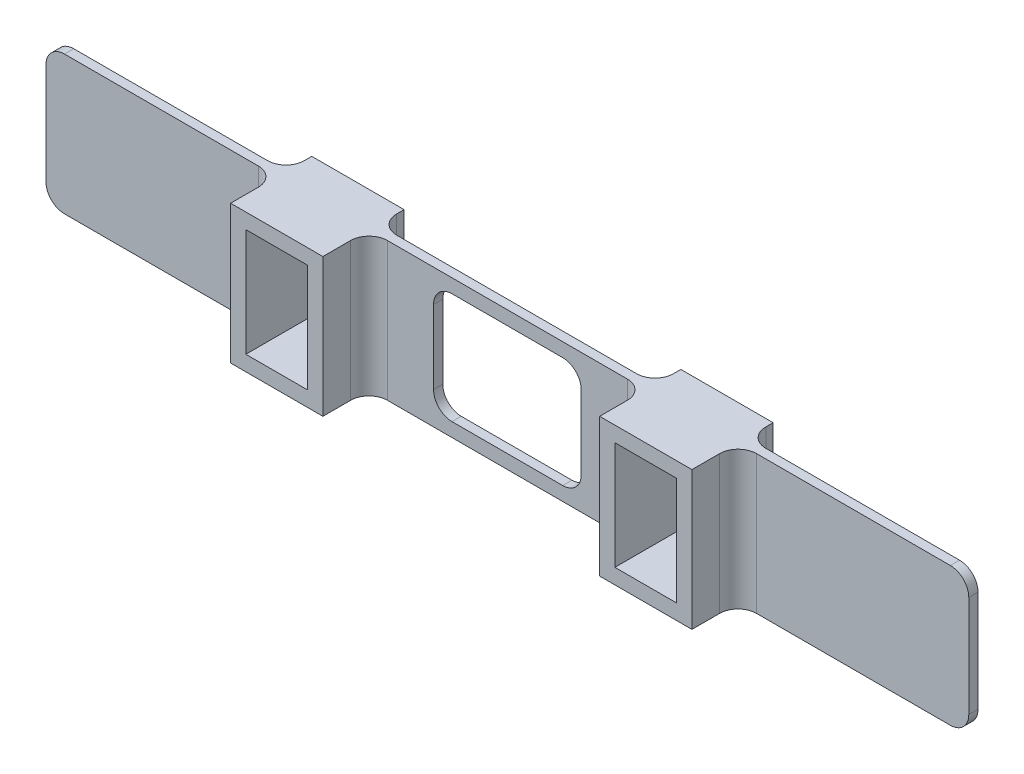
SolidWorks part; units mm, degrees
ref_plane "Front Plane" through (0, 0, 0) normal (0, 0, 1) x (1, 0, 0)
ref_plane "Top Plane" through (0, 0, 0) normal (0, 1, 0) x (1, 0, 0)
ref_plane "Right Plane" through (0, 0, 0) normal (1, 0, 0) x (0, 0, -1)
sketch "Sketch1" plane through (0, 0, 0) normal (0, 0, 1) x (1, 0, 0)
  line L1 (-250, -37.5) -> (250, -37.5)
  line L2 (-250, -37.5) -> (-250, 37.5)
  line L3 (-250, 37.5) -> (250, 37.5)
  line L4 (250, -37.5) -> (250, 37.5)
  line L5 (-250, -37.5) -> (250, 37.5) construction
  line L6 (-250, 37.5) -> (250, -37.5) construction
  point P0 (0, 0)
extrude "Boss-Extrude1" add sketch "Sketch1" along normal blind 5
sketch "Sketch2" plane through (0, 0, 5) normal (0, 0, 1) x (1, 0, 0)
  line L3 (-116.7208, -29.25) -> (-83.2208, -29.25)
  line L4 (-116.7208, -29.25) -> (-116.7208, 29.25)
  line L5 (-116.7208, 29.25) -> (-83.2208, 29.25)
  line L6 (-83.2208, -29.25) -> (-83.2208, 29.25)
  line L9 (83.25, -29.2517) -> (116.75, -29.2517)
  line L10 (83.25, -29.2517) -> (83.25, 29.2517)
  line L11 (83.25, 29.2517) -> (116.75, 29.2517)
  line L12 (116.75, -29.2517) -> (116.75, 29.2517)
extrude "Cut-Extrude1" cut sketch "Sketch2" against normal blind 5
sketch "Sketch3" plane through (0, 0, 5) normal (0, 0, 1) x (1, 0, 0)
  line L0 (250, 37.5) -> (-250, 37.5) construction
  line L1 (-116.7208, -29.25) -> (-83.2208, -29.25)
  line L2 (-116.7208, -29.25) -> (-116.7208, 29.25)
  line L3 (-116.7208, 29.25) -> (-83.2208, 29.25)
  line L4 (-83.2208, -29.25) -> (-83.2208, 29.25)
  line L5 (-116.7208, -29.25) -> (-83.2208, 29.25) construction
  line L6 (-116.7208, 29.25) -> (-83.2208, -29.25) construction
  line L7 (-124.9708, -37.5) -> (-74.9708, -37.5)
  line L8 (-124.9708, -37.5) -> (-124.9708, 37.5)
  line L9 (-124.9708, 37.5) -> (-74.9708, 37.5)
  line L10 (-74.9708, -37.5) -> (-74.9708, 37.5)
  line L11 (-124.9708, -37.5) -> (-74.9708, 37.5) construction
  line L12 (-124.9708, 37.5) -> (-74.9708, -37.5) construction
  line L14 (83.25, -29.2517) -> (116.75, -29.2517)
  line L15 (83.25, -29.2517) -> (83.25, 29.2517)
  line L16 (83.25, 29.2517) -> (116.75, 29.2517)
  line L17 (116.75, -29.2517) -> (116.75, 29.2517)
  line L18 (83.25, -29.2517) -> (116.75, 29.2517) construction
  line L19 (83.25, 29.2517) -> (116.75, -29.2517) construction
  line L20 (75, -37.5) -> (125, -37.5)
  line L21 (75, -37.5) -> (75, 37.5)
  line L22 (75, 37.5) -> (125, 37.5)
  line L23 (125, -37.5) -> (125, 37.5)
  line L24 (75, -37.5) -> (125, 37.5) construction
  line L25 (75, 37.5) -> (125, -37.5) construction
  point P0 (-99.9708, 0)
  point P5 (-99.9708, 0)
  point P13 (100, 0)
  point P18 (100, 0)
  dimension "D1" = 75
  dimension "D2" = 50
  dimension "D3" = 50
  dimension "D4" = 75
  dimension "D5" = 33.5
extrude "Boss-Extrude4" add sketch "Sketch3" along normal blind 25
sketch "Sketch5" plane through (0, 0, 0) normal (0, 0, -1) x (-1, 0, 0)
  line L1 (124.9708, 37.5) -> (74.9708, 37.5)
  line L2 (124.9708, 37.5) -> (124.9708, -37.5)
  line L3 (124.9708, -37.5) -> (74.9708, -37.5)
  line L4 (74.9708, 37.5) -> (74.9708, -37.5)
  line L5 (116.7208, 29.25) -> (83.2208, 29.25)
  line L6 (116.7208, 29.25) -> (116.7208, -29.25)
  line L7 (116.7208, -29.25) -> (83.2208, -29.25)
  line L8 (83.2208, 29.25) -> (83.2208, -29.25)
  line L9 (-83.25, 29.2517) -> (-116.75, 29.2517)
  line L10 (-83.25, 29.2517) -> (-83.25, -29.2517)
  line L11 (-83.25, -29.2517) -> (-116.75, -29.2517)
  line L12 (-116.75, 29.2517) -> (-116.75, -29.2517)
  line L13 (-75, 37.5) -> (-125, 37.5)
  line L14 (-75, 37.5) -> (-75, -37.5)
  line L15 (-75, -37.5) -> (-125, -37.5)
  line L16 (-125, 37.5) -> (-125, -37.5)
extrude "Boss-Extrude5" add sketch "Sketch5" along normal blind 14
fillet "Fillet1" radius 10 11 edges at (-250, -37.5, 2.5) (-250, 37.5, 2.5) (250, -37.5, 2.5) (250, 37.5, 2.5) (75, 0, 0) (-74.9708, 0, 0) (125, 0, 0) (125, 0, 5) (75, 0, 5) (-124.9708, 0, 5) (-74.9708, 0, 5)
fillet "Fillet2" radius 10 1 edges at (-124.9708, 0, 0)
sketch "Sketch6" plane through (0, 0, 5) normal (0, 0, 1) x (1, 0, 0)
  line L1 (-40, -30) -> (40, -30)
  line L2 (-40, -30) -> (-40, 30)
  line L3 (-40, 30) -> (40, 30)
  line L4 (40, -30) -> (40, 30)
  line L5 (-40, -30) -> (40, 30) construction
  line L6 (-40, 30) -> (40, -30) construction
  point P0 (0, 0)
extrude "Cut-Extrude3" cut sketch "Sketch6" against normal blind 380
fillet "Fillet3" radius 10 4 edges at (40, -30, 2.5) (-40, -30, 2.5) (40, 30, 2.5) (-40, 30, 2.5)
